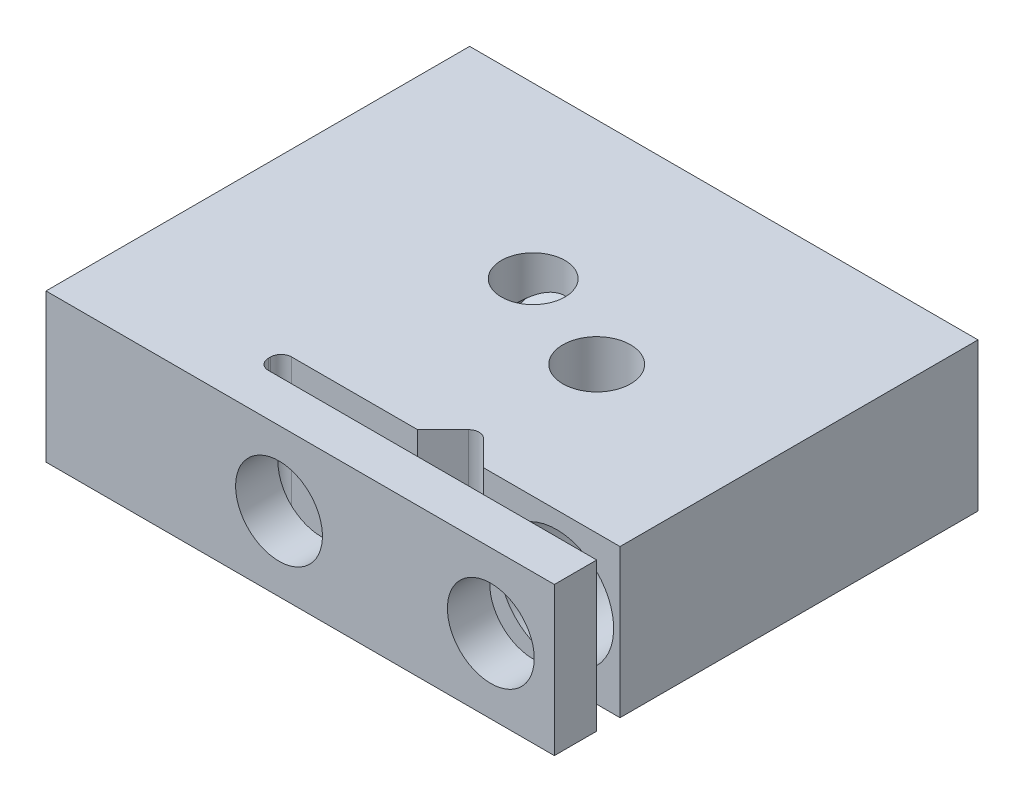
SolidWorks part; units mm, degrees
material "AISI 316 Annealed Stainless Steel Bar (SS)"
ref_plane "Front Plane" through (0, 0, 0) normal (0, 0, 1) x (1, 0, 0)
ref_plane "Top Plane" through (0, 0, 0) normal (0, 1, 0) x (1, 0, 0)
ref_plane "Right Plane" through (0, 0, 0) normal (1, 0, 0) x (0, 0, -1)
sketch "Sketch1" plane through (0, 0, 0) normal (0, 1, 0) x (1, 0, 0)
  line L1 (-6, 5) -> (6, 5)
  line L2 (-6, 5) -> (-6, -5)
  line L3 (-6, -5) -> (6, -5)
  line L4 (6, 5) -> (6, -5)
  point P4 (6, 0)
  point P6 (0, 5)
  dimension "D1" = 12
  dimension "D2" = 10
extrude "Boss-Extrude1" add sketch "Sketch1" along normal blind 3.5
sketch "Sketch2" plane through (0, 3.5, 0) normal (0, 1, 0) x (1, 0, 0)
  line L0 (2, -4) -> (6, -4)
  line L1 (6, -5) -> (6, 5) construction
  line L2 (6, -4) -> (6, -3.45)
  line L3 (6, -3.45) -> (2.7778, -3.45)
  line L4 (-6, -5) -> (6, -5) construction
  line L5 (2, -4) -> (-1.75, -4)
  line L6 (-2, -3.75) -> (-2, -3.7)
  line L7 (-1.75, -3.45) -> (1.2222, -3.45)
  line L8 (2.7778, -3.45) -> (2.1768, -2.849)
  line L9 (1.8232, -2.849) -> (1.2222, -3.45)
  circle A0 centre (2, -3.45) radius 0.55
  arc A1 (-2, -3.7) -> (-1.75, -3.45) centre (-1.75, -3.7) cw
  arc A2 (-1.75, -4) -> (-2, -3.75) centre (-1.75, -3.75) cw
  arc A3 (2.1768, -2.849) -> (1.8232, -2.849) centre (2, -3.0257) ccw
  point P6 (4, -4)
  point P22 (2, -2.6722)
  line M4 (6, -5) -> (6, 5)
  dimension "D1" = 1.1
  dimension "D5" = 0.25
  dimension "D6" = 0.25
  dimension "D2" = 1
  dimension "D3" = 4
  dimension "D4" = 8
extrude "Cut-Extrude1" cut sketch "Sketch2" against normal blind 3.5 contours A0 L0 L3 M4 | A0 | A0 L7 L6 L5 | L8 A3 L9 A0
hole_wizard "M2.5 Clearance Hole1" positions "Sketch3" profile "Sketch5" hole size "M2.5" standard "ISO" end condition up to next
sketch "Sketch3" plane through (0, 0, -5) normal (0, 0, -1) x (-1, 0, 0)
  line L1 (-6, 3.5) -> (-6, 0) construction
  line L2 (-6, 3.5) -> (-6, 0)
  point P0 (-4.5, 1.75)
  point P7 (-6, 1.75)
  dimension "D1" = 1.5
sketch "Sketch5" plane through (4.5, 1.75, -5) normal (1, 0, 0) x (0, 1, 0)
  line L0 (0, 0) -> (0, 8.45)
  line L1 (0, 8.45) -> (1.35, 8.45)
  line L2 (1.35, 8.45) -> (1.35, 0)
  line L5 (1.35, 0) -> (0, 0)
  line L11 (0, -6.35) -> (0, 107.95) construction
  dimension "Thru Hole Dia." = 2.7
  dimension "Thru Hole Depth" = 8.45
hole_wizard "M2.5 Tapped Hole1" positions "Sketch6" profile "Sketch7" tap size "M2.5" standard "ISO" end condition up to next
sketch "Sketch6" plane through (0, 0, 5) normal (0, 0, 1) x (1, 0, 0)
  circle A0 centre (4.5, 1.75) radius 1.35 construction
  circle A1 centre (4.5, 1.75) radius 1.35
  point P0 (4.5, 1.75)
sketch "Sketch7" plane through (4.5, 1.75, 5) normal (1, 0, 0) x (0, -1, 0)
  line L0 (0, 0) -> (0, 1)
  line L1 (0, 1) -> (1.025, 1)
  line L2 (1.025, 1) -> (1.025, 0)
  line L5 (1.025, 0) -> (0, 0)
  line L11 (0, -6.35) -> (0, 107.95) construction
  dimension "Thru Tap Drill Dia." = 2.05
  dimension "Thru Tap Drill Depth" = 1
cosmetic thread "Hole Thread1" parameters "D2"=2.5
hole_wizard "Ø1.5 (1.5) Diameter Hole1" positions "Sketch8" profile "Sketch9" hole size "Ø1.5" standard "ISO" end condition up to next
sketch "Sketch8" plane through (0, 3.5, 0) normal (0, 1, 0) x (1, 0, 0)
  line L0 (6, -3.45) -> (6, 5) construction
  line L1 (6, 5) -> (-6, 5) construction
  point P0 (-0.5, 1)
  dimension "D1" = 6.5
  dimension "D2" = 4
sketch "Sketch9" plane through (-0.5, 3.5, -1) normal (1, 0, 0) x (0, 0, 1)
  line L0 (0, 0) -> (0, 3.5)
  line L1 (0, 3.5) -> (0.75, 3.5)
  line L2 (0.75, 3.5) -> (0.75, 0)
  line L5 (0.75, 0) -> (0, 0)
  line L11 (0, -6.35) -> (0, 107.95) construction
  dimension "Thru Hole Dia." = 1.5
  dimension "Thru Hole Depth" = 3.5
hole_wizard "M2.5 Tapped Hole2" positions "Sketch10" profile "Sketch11" tap size "M2.5" standard "ISO" end condition through all
sketch "Sketch10" plane through (0, 0, -5) normal (0, 0, -1) x (-1, 0, 0)
  line L0 (-6, 3.5) -> (-6, 0) construction
  line L1 (-6, 3.5) -> (-6, 0)
  point P0 (0.5, 1.75)
  point P5 (-6, 1.75)
  dimension "D1" = 6.5
sketch "Sketch11" plane through (-0.5, 1.75, -5) normal (1, 0, 0) x (0, 1, 0)
  line L0 (0, 0) -> (0, 10)
  line L1 (0, 10) -> (1.025, 10)
  line L2 (1.025, 10) -> (1.025, 0)
  line L5 (1.025, 0) -> (0, 0)
  line L11 (0, -6.35) -> (0, 107.95) construction
  dimension "Thru Tap Drill Dia." = 2.05
  dimension "Thru Tap Drill Depth" = 10
cosmetic thread "Hole Thread2" parameters "D2"=2.5
hole_wizard "M2.5 Tapped Hole4" positions "Sketch13" profile "Sketch14" tap size "M2.5" standard "ISO"
sketch "Sketch13" plane through (-6, 0, 0) normal (-1, 0, 0) x (0, 0, 1)
  line L0 (-5, 3.5) -> (-5, 0) construction
  line L1 (-5, 3.5) -> (-5, 0)
  line L2 (5, 3.5) -> (5, 0) construction
  point P0 (-2.5, 1.75)
  point P2 (2.5, 1.75)
  point P7 (-5, 1.75)
  dimension "D1" = 2.5
  dimension "D2" = 2.5
sketch "Sketch14" plane through (-6, 1.75, -2.5) normal (0, 1, 0) x (0, 0, 1)
  line L0 (0, 0) -> (0, 5.6159)
  line L1 (0, 5.6159) -> (1.025, 5)
  line L2 (1.025, 5) -> (1.025, 0)
  line L5 (1.025, 0) -> (0, 0)
  line L10 (0, 5.6159) -> (-1.025, 5) construction
  line L11 (0, -6.35) -> (0, 107.95) construction
  dimension "Tap Drill Dia." = 2.05
  dimension "Tap Drill Depth" = 5
  dimension "Drill Angle" = 118
cosmetic thread "Hole Thread5" parameters "D1"=4, "D2"=2.1
cosmetic thread "Hole Thread6" parameters "D1"=4, "D2"=2.1
hole_wizard "M2 Tapped Hole1" positions "Sketch17" profile "Sketch18" tap size "M2" standard "ISO" end condition through all
sketch "Sketch17" plane through (0, 0, 0) normal (0, -1, 0) x (-1, 0, 0)
  line L0 (6, -5) -> (-6, -5) construction
  arc A0 (-1.8232, -2.849) -> (-2.1768, -2.849) centre (-2, -3.0257) ccw construction
  arc A1 (-1.8232, -2.849) -> (-2.1768, -2.849) centre (-2, -3.0257) ccw
  point P0 (-2, 0)
  dimension "D1" = 5
sketch "Sketch18" plane through (2, 0, 0) normal (1, 0, 0) x (0, 0, -1)
  line L0 (0, 0) -> (0, 3.5)
  line L1 (0, 3.5) -> (0.8, 3.5)
  line L2 (0.8, 3.5) -> (0.8, 0)
  line L5 (0.8, 0) -> (0, 0)
  line L11 (0, -6.35) -> (0, 107.95) construction
  dimension "Thru Tap Drill Dia." = 1.6
  dimension "Thru Tap Drill Depth" = 3.5
cosmetic thread "Hole Thread8" parameters "D2"=2
